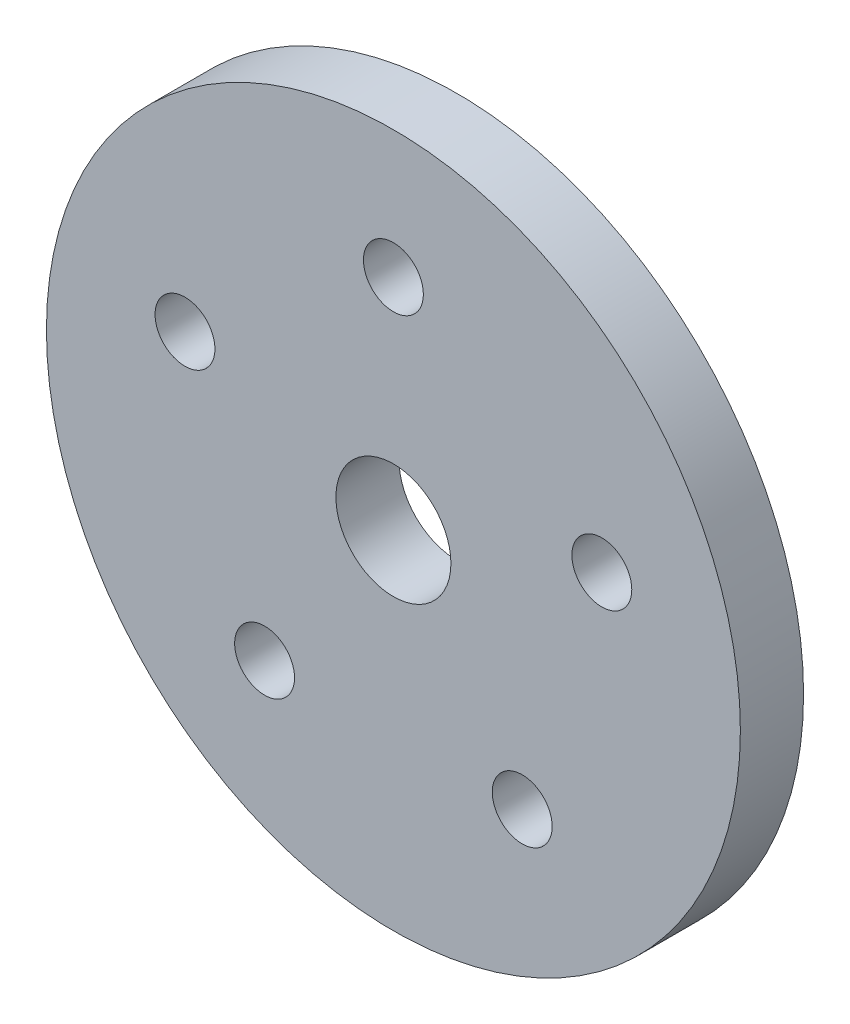
SolidWorks part; units mm, degrees
ref_plane "Front Plane" through (0, 0, 0) normal (0, 0, 1) x (1, 0, 0)
ref_plane "Top Plane" through (0, 0, 0) normal (0, 1, 0) x (1, 0, 0)
ref_plane "Right Plane" through (0, 0, 0) normal (1, 0, 0) x (0, 0, -1)
sketch "Sketch1" plane through (0, 0, 0) normal (0, 0, 1) x (1, 0, 0)
  line L0 (0, 0) -> (0, 24.13) construction
  circle A0 centre (0, 0) radius 24.13
  circle A1 centre (0, 15.24) radius 2.0828
  circle A2 centre (14.4941, 4.7094) radius 2.0828
  circle A3 centre (8.9578, -12.3294) radius 2.0828
  circle A4 centre (-8.9578, -12.3294) radius 2.0828
  circle A5 centre (-14.4941, 4.7094) radius 2.0828
  circle A6 centre (0, 0) radius 4
  point P17 (0, 0)
  dimension "D1" = 48.26
  dimension "D2" = 4.1656
  dimension "D5" = 8
  dimension "D3" = 15.24
  dimension "D4" = 5
extrude "Boss-Extrude1" add sketch "Sketch1" along normal blind 4.3942
